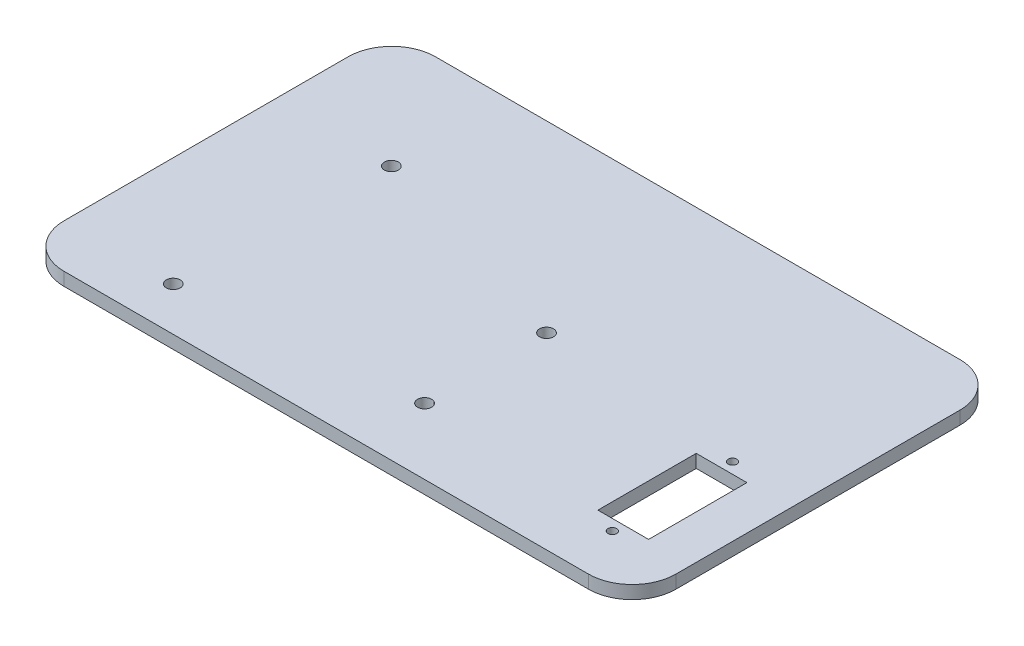
SolidWorks part; units mm, degrees
ref_plane "Front Plane" through (0, 0, 0) normal (0, 0, 1) x (1, 0, 0)
ref_plane "Top Plane" through (0, 0, 0) normal (0, 1, 0) x (1, 0, 0)
ref_plane "Right Plane" through (0, 0, 0) normal (1, 0, 0) x (0, 0, -1)
sketch "Sketch3" plane through (0, 0, 0) normal (0, 1, 0) x (1, 0, 0)
  line L1 (-70, 42.5) -> (70, 42.5)
  line L2 (-70, 42.5) -> (-70, -42.5)
  line L3 (-70, -42.5) -> (70, -42.5)
  line L4 (70, 42.5) -> (70, -42.5)
  line L5 (-70, 42.5) -> (70, -42.5) construction
  line L6 (-70, -42.5) -> (70, 42.5) construction
  point P0 (0, 0)
  dimension "D1" = 140
  dimension "D2" = 85
extrude "Boss-Extrude1" add sketch "Sketch3" along normal blind 3 contours L1 L4 L3 L2
sketch "Sketch4" plane through (0, 3, 0) normal (0, 1, 0) x (1, 0, 0)
  line L1 (-70, 42.5) -> (-70, -42.5) construction
  line L2 (-70, -42.5) -> (70, -42.5) construction
  line L3 (-45, 15.8) -> (-45, -32.5) construction
  line L5 (-70, 42.5) -> (-70, -42.5) construction
  line L6 (7.4, 0.5) -> (7.4, -27.4) construction
  line L7 (70, 42.5) -> (70, -42.5) construction
  circle A0 centre (-43.4, 15.8) radius 1.6
  circle A1 centre (7.4, 0.5) radius 1.6
  circle A2 centre (-45, -32.5) radius 1.6
  circle A3 centre (7.4, -27.4) radius 1.6
  dimension "D1" = 3.2
  dimension "D2" = 25
  dimension "D3" = 10
  dimension "D4" = 48.3
  dimension "D5" = 5.1
  dimension "D6" = 27.9
  dimension "D7" = 50.8
extrude "Cut-Extrude1" cut sketch "Sketch4" against normal blind 3
sketch "Sketch5" [suppressed] plane through (0, 3, 0) normal (0, 1, 0) x (1, 0, 0)
  line L0 (-47, -47) -> (47, -47) construction
  line L1 (21.45, -2.8) -> (33.45, -2.8)
  line L2 (21.45, -2.8) -> (21.45, 11.2)
  line L3 (21.45, 11.2) -> (33.45, 11.2)
  line L4 (33.45, -2.8) -> (33.45, 11.2)
  line L5 (47, 47) -> (47, -47) construction
  dimension "D1" = 12
  dimension "D2" = 14
  dimension "D3" = 44.2
  dimension "D4" = 13.55
extrude "Cut-Extrude2" [suppressed] cut sketch "Sketch5" against normal blind 10
sketch "Sketch6" [suppressed] plane through (0, 3, 0) normal (0, 1, 0) x (1, 0, 0)
  line L0 (-47, 47) -> (47, 47) construction
  line L1 (22.2, 30) -> (32.7, 30)
  line L2 (22.2, 30) -> (22.2, 39)
  line L3 (22.2, 39) -> (32.7, 39)
  line L4 (32.7, 30) -> (32.7, 39)
  line L5 (47, 47) -> (47, -47) construction
  dimension "D1" = 9
  dimension "D2" = 10.5
  dimension "D3" = 8
  dimension "D4" = 14.3
extrude "Cut-Extrude3" [suppressed] cut sketch "Sketch6" against normal blind 10
fillet "Fillet1" radius 10 1 edges at (-70, 1.5, 42.5)
fillet "Fillet2" radius 10 1 edges at (-70, 1.5, -42.5)
fillet "Fillet3" radius 10 1 edges at (70, 1.5, -42.5)
fillet "Fillet4" radius 10 1 edges at (70, 1.5, 42.5)
sketch "Sketch7" plane through (0, 3, 0) normal (0, 1, 0) x (1, 0, 0)
  line L0 (70, 32.5) -> (70, -32.5) construction
  line L1 (60, -28.75) -> (48.4, -28.75)
  line L2 (60, -28.75) -> (60, -6.25)
  line L3 (60, -6.25) -> (48.4, -6.25)
  line L4 (48.4, -28.75) -> (48.4, -6.25)
  line L5 (60, -28.75) -> (48.4, -6.25) construction
  line L6 (60, -6.25) -> (48.4, -28.75) construction
  line L7 (-60, -42.5) -> (60, -42.5) construction
  line L8 (54.2, -31.25) -> (54.2, -3.75) construction
  line L9 (60, -17.5) -> (48.4, -17.5) construction
  circle A0 centre (54.2, -31.25) radius 1
  circle A1 centre (54.2, -3.75) radius 1
  point P0 (54.2, -17.5)
  dimension "D5" = 2
  dimension "D6" = 27.5
  dimension "D1" = 10
  dimension "D2" = 11.6
  dimension "D3" = 22.5
  dimension "D4" = 25
extrude "Cut-Extrude4" cut sketch "Sketch7" against normal blind 3
sketch "Sketch8" plane through (0, 0, 0) normal (0, -1, 0) x (1, 0, 0)
  line L0 (70, -32.5) -> (70, 32.5) construction
  line L1 (-60, 42.5) -> (60, 42.5) construction
  line L3 (39.74, 26.2) -> (39.74, -1.3) construction
  circle A0 centre (18.24, 12.45) radius 1.6
  circle A1 centre (39.74, 26.2) radius 1.6
  circle A2 centre (39.74, -1.3) radius 1.6
  dimension "D1" = 27.5
  dimension "D2" = 16.3
  dimension "D4" = 30.26
  dimension "D3" = 30.05
  dimension "D5" = 21.5
